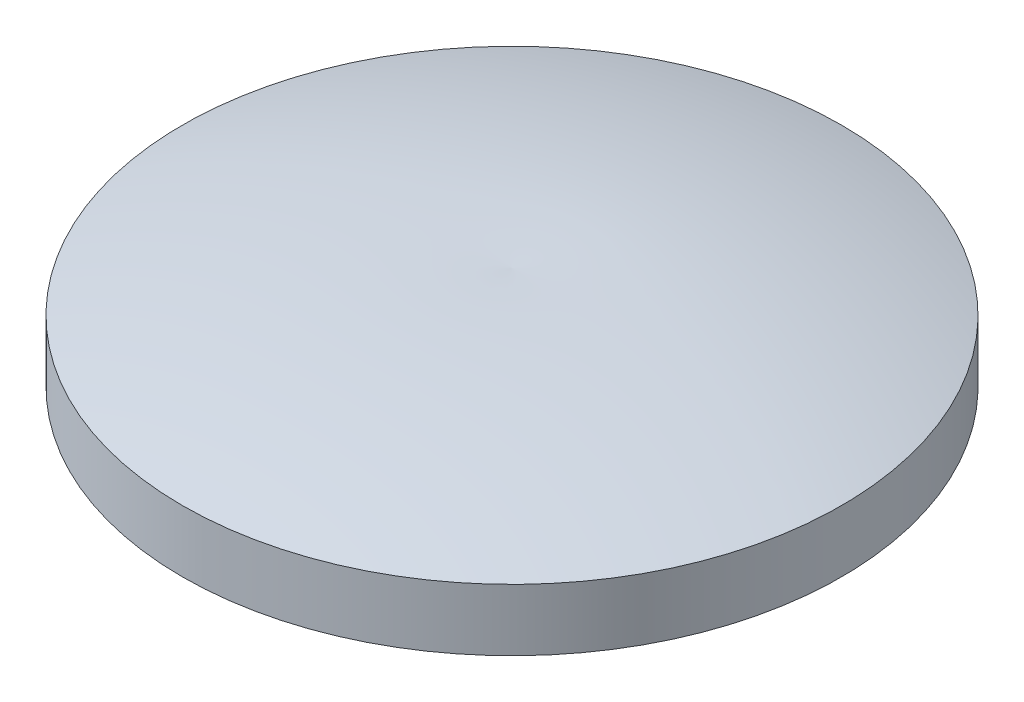
SolidWorks part; units mm, degrees
ref_plane "Front Plane" through (0, 0, 0) normal (0, 0, 1) x (1, 0, 0)
ref_plane "Top Plane" through (0, 0, 0) normal (0, 1, 0) x (1, 0, 0)
ref_plane "Right Plane" through (0, 0, 0) normal (1, 0, 0) x (0, 0, -1)
sketch "Sketch1" plane through (0, 0, 0) normal (0, 0, 1) x (1, 0, 0)
  line L0 (0, 0) -> (0, 6.35)
  line L1 (0, 0) -> (-20.32, 0)
  line L2 (-20.32, 0) -> (-20.32, 3.81)
  arc A0 (-20.32, 3.81) -> (0, 6.35) centre (-3.1861, -50.7111) cw
  dimension "D4" = 57.15
  dimension "D1" = 20.32
  dimension "D2" = 6.35
  dimension "D3" = 3.81
revolve "Revolve1" add sketch "Sketch1" angle 360 about L0
